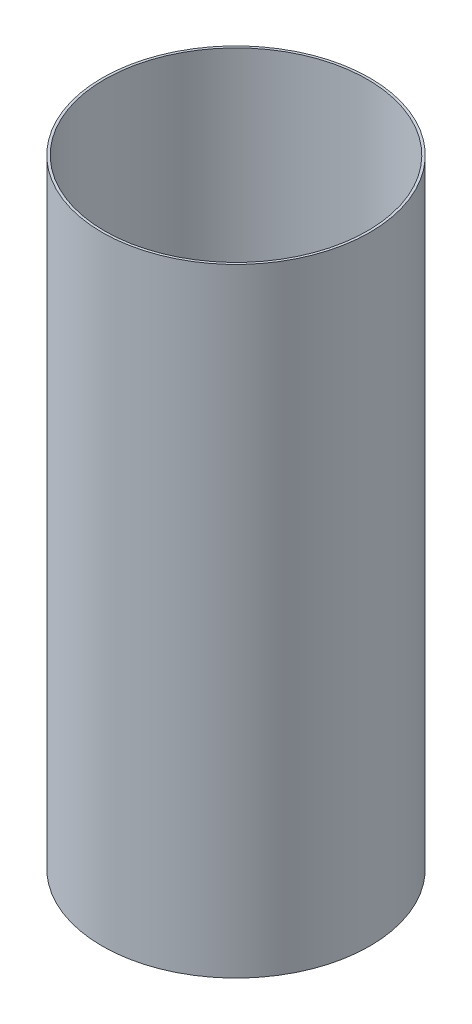
SolidWorks part; units mm, degrees
ref_plane "Front Plane" through (0, 0, 0) normal (0, 0, 1) x (1, 0, 0)
ref_plane "Top Plane" through (0, 0, 0) normal (0, 1, 0) x (1, 0, 0)
ref_plane "Right Plane" through (0, 0, 0) normal (1, 0, 0) x (0, 0, -1)
sketch "Sketch1" plane through (0, 0, 0) normal (0, 1, 0) x (1, 0, 0)
  circle A0 centre (0, 0) radius 54
  circle A1 centre (0, 0) radius 55
  dimension "D1" = 108
  dimension "D2" = 110
extrude "Boss-Extrude1" add sketch "Sketch1" along normal blind 254
